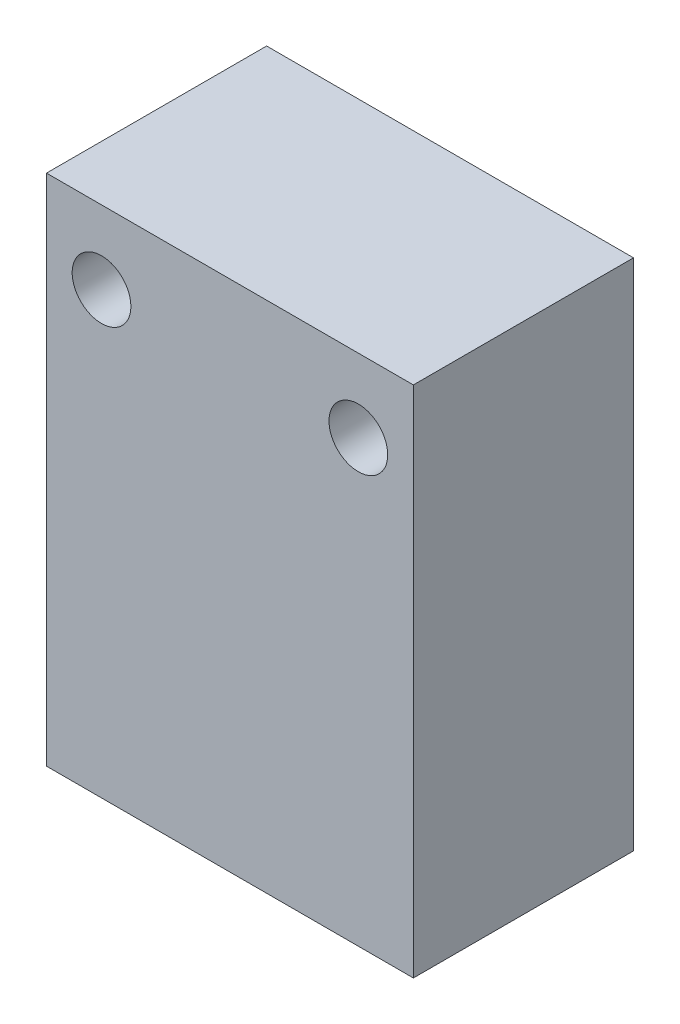
SolidWorks part; units mm, degrees
ref_plane "前视基准面" through (0, 0, 0) normal (0, 0, 1) x (1, 0, 0)
ref_plane "上视基准面" through (0, 0, 0) normal (0, 1, 0) x (1, 0, 0)
ref_plane "右视基准面" through (0, 0, 0) normal (1, 0, 0) x (0, 0, -1)
sketch "草图1" plane through (0, 0, 0) normal (0, 0, 1) x (1, 0, 0)
  line L1 (-12.9851, 11.7164) -> (7.0149, 11.7164)
  line L2 (-12.9851, 11.7164) -> (-12.9851, -16.2836)
  line L3 (-12.9851, -16.2836) -> (7.0149, -16.2836)
  line L4 (7.0149, 11.7164) -> (7.0149, -16.2836)
  dimension "D1" = 20
  dimension "D2" = 28
extrude "凸台-拉伸1" add sketch "草图1" along normal blind 12
sketch "草图2" plane through (0, 0, 12) normal (0, 0, 1) x (1, 0, 0)
  circle A0 centre (-9.9851, 7.7164) radius 1.6
  circle A1 centre (4.0149, 7.7164) radius 1.6
  dimension "D4" = 3.2
  dimension "D5" = 3.2
extrude "切除-拉伸1" cut sketch "草图2" against normal through all
